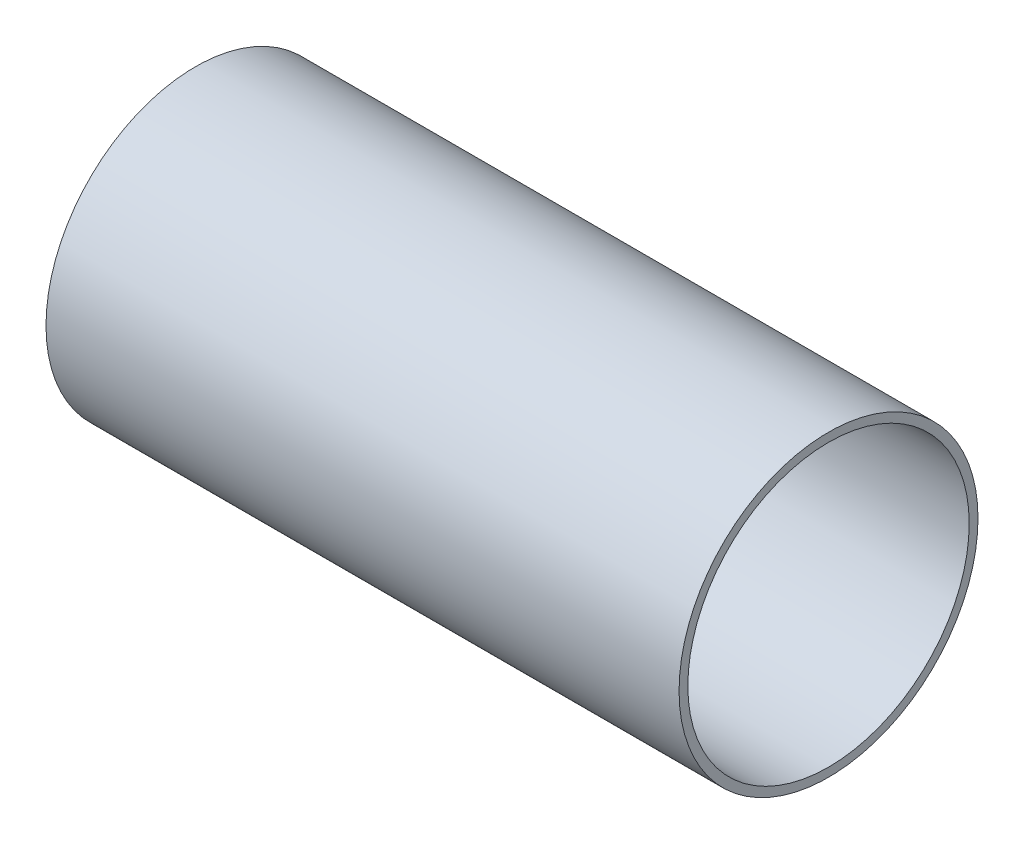
SolidWorks part; units mm, degrees
material "PVC Rigid"
ref_plane "Front Plane" through (0, 0, 0) normal (0, 0, 1) x (1, 0, 0)
ref_plane "Top Plane" through (0, 0, 0) normal (0, 1, 0) x (1, 0, 0)
ref_plane "Right Plane" through (0, 0, 0) normal (1, 0, 0) x (0, 0, -1)
sketch "Sketch1" plane through (0, 0, 0) normal (1, 0, 0) x (0, 0, -1)
  circle A0 centre (0, 0) radius 53.975
  circle A1 centre (0, 0) radius 50.8
  dimension "D1" = 101.6
  dimension "D2" = 3.175
extrude "Boss-Extrude1" add sketch "Sketch1" along normal blind 228.6
